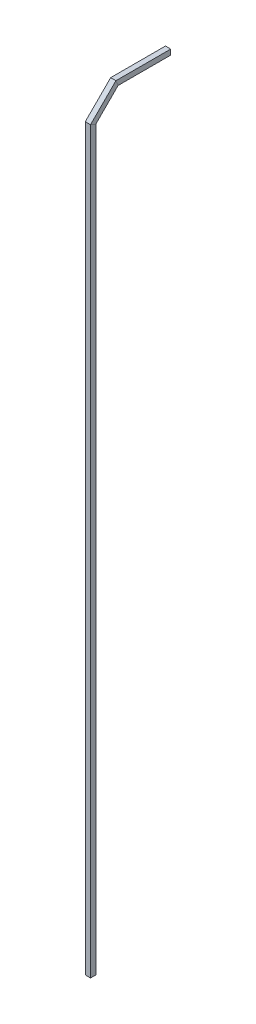
SolidWorks part; units mm, degrees
ref_plane "Front" through (0, 0, 0) normal (0, 0, 1) x (1, 0, 0)
ref_plane "Top" through (0, 0, 0) normal (0, 1, 0) x (1, 0, 0)
ref_plane "Right" through (0, 0, 0) normal (1, 0, 0) x (0, 0, -1)
sketch "草图1" plane through (0, 0, 0) normal (0, 1, 0) x (1, 0, 0)
  line L0 (0, 0) -> (43.8583, 0) construction
  line L1 (-5, 5) -> (5, 5)
  line L2 (-5, 5) -> (-5, -5)
  line L3 (-5, -5) -> (5, -5)
  line L4 (5, 5) -> (5, -5)
  line L5 (0, 0) -> (0, 44.3867) construction
  dimension "D1" = 10
  dimension "D2" = 5
  dimension "D3" = 10
  dimension "D4" = 5
sketch "草图3" plane through (0, 0, 0) normal (1, 0, 0) x (0, 0, -1)
  line L0 (5, 0) -> (5, 1400)
  line L1 (0, 0) -> (44.3867, 0) construction
  line L2 (5, 0) -> (-5, 0) construction
  line L3 (5, 1400) -> (47.4264, 1442.4264)
  line L4 (47.4264, 1442.4264) -> (147.4264, 1442.4264)
  dimension "D1" = 1400
  dimension "D2" = 60
  dimension "D3" = 100
sweep "扫描2" add profiles "草图1" path "草图3"
